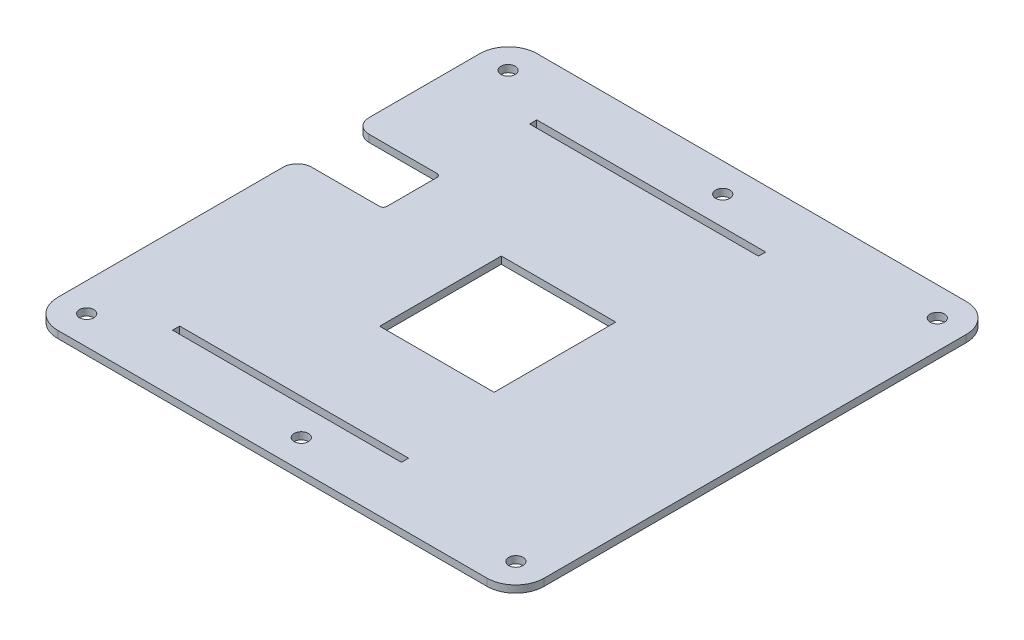
SolidWorks part; units mm, degrees
material "6061-T6 (SS)"
ref_plane "Front Plane" through (0, 0, 0) normal (0, 0, 1) x (1, 0, 0)
ref_plane "Top Plane" through (0, 0, 0) normal (0, 1, 0) x (1, 0, 0)
ref_plane "Right Plane" through (0, 0, 0) normal (1, 0, 0) x (0, 0, -1)
sketch "Sketch1" plane through (0, 0, 0) normal (0, 1, 0) x (1, 0, 0)
  line L1 (-127, 106.3625) -> (127, 106.3625)
  line L2 (-127, 106.3625) -> (-127, -106.3625)
  line L3 (-127, -106.3625) -> (127, -106.3625)
  line L4 (127, 106.3625) -> (127, -106.3625)
  line L5 (-127, 106.3625) -> (127, -106.3625) construction
  line L6 (-127, -106.3625) -> (127, 106.3625) construction
  line L7 (-50.8, 80.8355) -> (50.8, 80.8355) construction
  line L8 (-50.8, 80.8355) -> (50.8, 80.8355)
  line L9 (-50.8, 80.8355) -> (-50.8, 77.6605)
  line L10 (-50.8, 77.6605) -> (50.8, 77.6605)
  line L11 (50.8, 80.8355) -> (50.8, 77.6605)
  line L12 (-50.8, 77.6605) -> (50.8, 77.6605) construction
  line L13 (50.8, 77.6605) -> (50.8, 80.8355) construction
  line L14 (-50.8, 77.6605) -> (-50.8, 80.8355) construction
  line L15 (-50.8, -80.8355) -> (50.8, -80.8355) construction
  line L16 (-50.8, -77.6605) -> (50.8, -77.6605)
  line L17 (-50.8, -77.6605) -> (-50.8, -80.8355)
  line L18 (-50.8, -80.8355) -> (50.8, -80.8355)
  line L19 (44.45, 20.6375) -> (-6.35, 20.6375)
  line L20 (44.45, 20.6375) -> (44.45, -33.3375)
  line L21 (-107.95, 12.7) -> (-50.8, 12.7)
  line L22 (-107.95, 12.7) -> (-107.95, 38.1)
  line L23 (-107.95, 38.1) -> (-50.8, 38.1)
  line L24 (-50.8, 12.7) -> (-50.8, 38.1)
  line L25 (-107.95, 12.7) -> (-50.8, 38.1) construction
  line L26 (-107.95, 38.1) -> (-50.8, 12.7) construction
  line L27 (44.45, -33.3375) -> (-6.35, -33.3375)
  line L28 (50.8, -77.6605) -> (50.8, -80.8355)
  line L29 (-6.35, 20.6375) -> (-6.35, -33.3375)
  line L30 (-50.8, -80.8355) -> (-50.8, -77.6605) construction
  line L31 (-50.8, -77.6605) -> (50.8, -77.6605) construction
  line L32 (50.8, -80.8355) -> (50.8, -77.6605) construction
  line L33 (44.45, 20.6375) -> (-6.35, -33.3375) construction
  line L34 (44.45, -33.3375) -> (-6.35, 20.6375) construction
  point P0 (0, 0)
  point P20 (-79.375, 25.4)
  point P35 (19.05, -6.35)
  dimension "D1" = 254
  dimension "D2" = 25.4
  dimension "D3" = 53.975
  dimension "D4" = 212.725
  dimension "D5" = 25.4
  dimension "D6" = 57.15
  dimension "D7" = 50.8
  dimension "D8" = 50.8
  dimension "D9" = 6.35
  dimension "D10" = 19.05
extrude "Boss-Extrude1" add sketch "Sketch1" along normal blind 3.175
sketch "Sketch3" plane through (0, 3.175, 0) normal (0, 1, 0) x (1, 0, 0)
  line L0 (127, 106.3625) -> (-127, 106.3625) construction
  line L1 (-88.9, 106.3625) -> (-127, 106.3625)
  line L2 (-88.9, 106.3625) -> (-88.9, -106.3625)
  line L3 (-88.9, -106.3625) -> (-127, -106.3625)
  line L4 (-127, 106.3625) -> (-127, -106.3625)
  line L5 (-127, 106.3625) -> (-127, -106.3625) construction
  line L6 (-127, -106.3625) -> (127, -106.3625) construction
  dimension "D1" = 38.1
extrude "Cut-Extrude2" cut sketch "Sketch3" against normal through all
fillet "Fillet1" radius 12.7 4 edges at (127, 1.5875, -106.3625) (127, 1.5875, 106.3625) (-88.9, 1.5875, -106.3625) (-88.9, 1.5875, 106.3625)
sketch "Sketch2" plane through (0, 3.175, 0) normal (0, 1, 0) x (1, 0, 0)
  line L0 (127, -93.6625) -> (127, 93.6625) construction
  line L1 (-88.9, -93.6625) -> (-88.9, 12.7) construction
  line L2 (-88.9, -80.8355) -> (127, -80.8355) construction
  line L4 (-88.9, 80.8355) -> (185.6093, 80.8355) construction
  line L5 (114.3, -93.5355) -> (-76.2, -93.5355) construction
  line L6 (114.3, 93.5355) -> (-76.2, 93.5355) construction
  circle A0 centre (114.3, 93.5355) radius 3.175
  circle A1 centre (114.3, -93.5355) radius 3.175
  circle A2 centre (-76.2, -93.5355) radius 3.175
  circle A3 centre (-76.2, 93.5355) radius 3.175
  circle A4 centre (19.05, -93.5355) radius 3.175
  circle A5 centre (19.05, 93.5355) radius 3.175
  dimension "D1" = 6.35
  dimension "D2" = 12.7
  dimension "D3" = 12.7
  dimension "D4" = 12.7
  dimension "D5" = 12.7
extrude "Cut-Extrude1" cut sketch "Sketch2" against normal through all and the other way through all
fillet "Fillet2" radius 1.5875 2 edges at (-50.8, 1.5875, -12.7) (-50.8, 1.5875, -38.1)
fillet "Fillet3" radius 6.35 2 edges at (-88.9, 1.5875, -12.7) (-88.9, 1.5875, -38.1)
